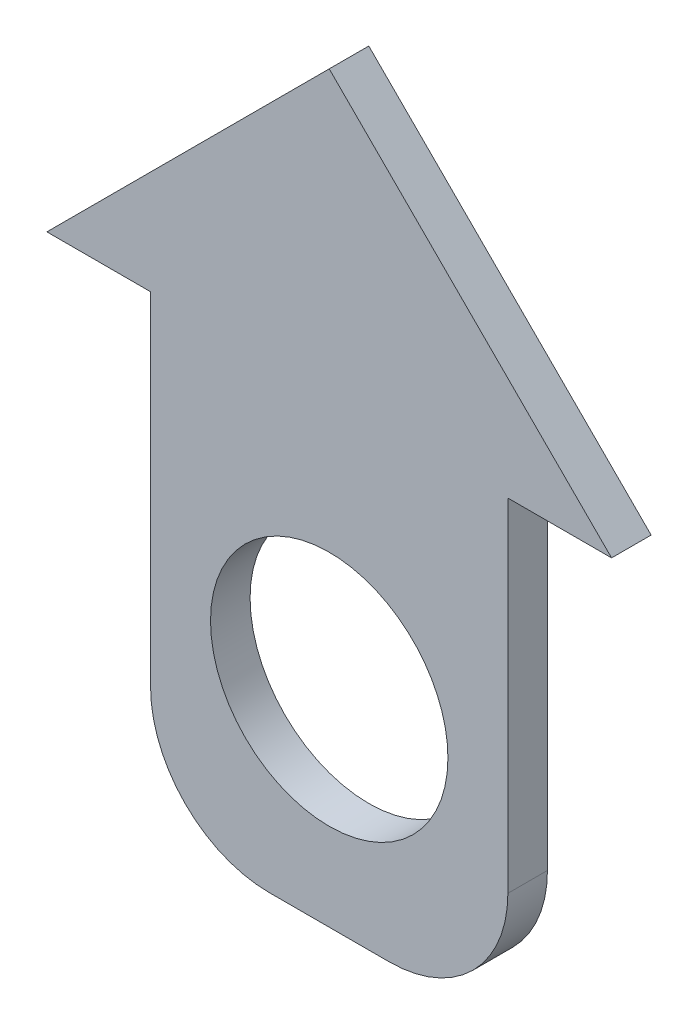
SolidWorks part; units mm, degrees
ref_plane "Front" through (0, 0, 0) normal (0, 0, 1) x (1, 0, 0)
ref_plane "Top" through (0, 0, 0) normal (0, 1, 0) x (1, 0, 0)
ref_plane "Right" through (0, 0, 0) normal (1, 0, 0) x (0, 0, -1)
sketch "Sketch1" plane through (0, 0, 0) normal (0, 0, 1) x (1, 0, 0)
  line L0 (0, 0) -> (0, -5.208) construction
  line L1 (-4.5151, -5.208) -> (4.5151, -5.208)
  line L2 (4.5151, -5.208) -> (4.5151, 6.4428)
  line L3 (4.5151, 6.4428) -> (7.1357, 6.4428)
  line L4 (7.1357, 6.4428) -> (0, 13.5785)
  line L5 (0, 13.5785) -> (-7.1357, 6.4428)
  line L6 (-7.1357, 6.4428) -> (-4.5151, 6.4428)
  line L7 (-4.5151, 6.4428) -> (-4.5151, -5.208)
  circle A0 centre (0, 0) radius 3
  point P7 (0, -5.208)
  point P13 (0, 0)
extrude "Boss-Extrude1" add sketch "Sketch1" along normal blind 1
fillet "Fillet1" radius 3 2 edges at (-4.5151, -5.208, 0.5) (4.5151, -5.208, 0.5)
sketch "Sketch2" plane through (0, 0, 0) normal (0, 0, -1) x (-1, 0, 0)
  line L0 (1, 2.8284) -> (1, 4.2101)
  line L1 (-1, 2.8284) -> (-1, 4.2101)
  line L2 (-1, 4.2101) -> (1, 4.2101)
  line L3 (0, 4.2101) -> (0, 3)
  arc A0 (1, 2.8284) -> (-1, 2.8284) centre (0, 0) ccw
  circle M14 centre (0, 0) radius 3
extrude "Boss-Extrude2" add sketch "Sketch2" along normal blind 1 contours L2 L3 L0 M14 | L3 L2 L1 M14
